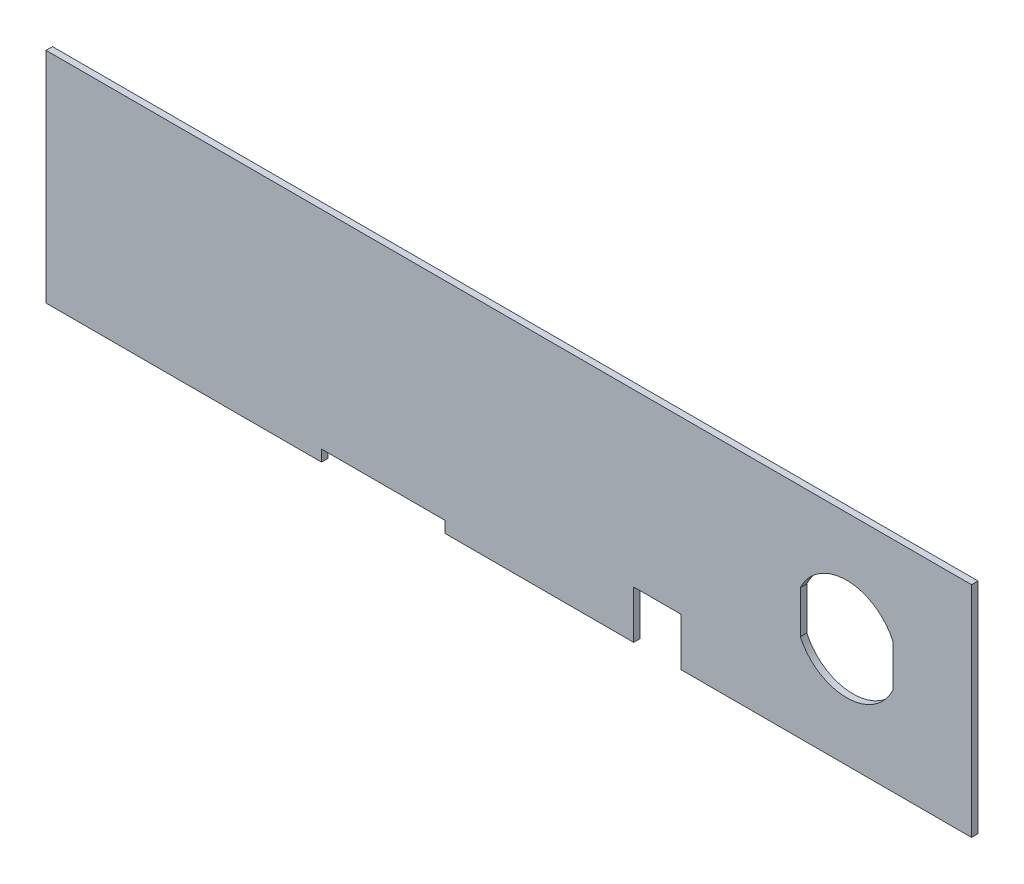
SolidWorks part; units mm, degrees
ref_plane "Front Plane" through (0, 0, 0) normal (0, 0, 1) x (1, 0, 0)
ref_plane "Top Plane" through (0, 0, 0) normal (0, 1, 0) x (1, 0, 0)
ref_plane "Right Plane" through (0, 0, 0) normal (1, 0, 0) x (0, 0, -1)
sketch "Sketch1" plane through (0, 0, 0) normal (0, 0, 1) x (1, 0, 0)
  line L0 (161.29, 0) -> (174.3202, 0)
  line L1 (0, 60.071) -> (254, 60.071)
  line L2 (0, 60.071) -> (0, 0)
  line L3 (0, 0) -> (254, 0)
  line L4 (254, 60.071) -> (254, 0)
  line L5 (92.5322, 0) -> (92.5322, 60.071) construction
  line L6 (75.6158, 3.1115) -> (109.4486, 3.1115)
  line L7 (75.6158, 3.1115) -> (75.6158, 0)
  line L8 (161.29, 0) -> (161.29, 13.1699)
  line L9 (161.29, 13.1699) -> (174.3202, 13.1699)
  line L10 (174.3202, 0) -> (174.3202, 13.1699)
  line L11 (75.6158, 0) -> (109.4486, 0)
  line L12 (109.4486, 3.1115) -> (109.4486, 0)
  line L13 (232.41, 24.2156) -> (232.41, 35.8554)
  line L14 (207.01, 24.2156) -> (207.01, 35.8554)
  circle A0 centre (219.71, 30.0355) radius 20.32 construction
  arc A1 (232.41, 35.8554) -> (207.01, 35.8554) centre (219.71, 30.0355) ccw
  arc A2 (207.01, 24.2156) -> (232.41, 24.2156) centre (219.71, 30.0355) ccw
  dimension "D3" = 40.64
  dimension "D6" = 27.94
  dimension "D1" = 254
  dimension "D2" = 60.071
  dimension "D4" = 13.1699
  dimension "D5" = 13.0302
  dimension "D7" = 219.71
  dimension "D8" = 161.29
  dimension "D9" = 30.0355
  dimension "D10" = 3.1115
  dimension "D11" = 33.8328
  dimension "D12" = 92.5322
  dimension "D13" = 25.4
extrude "Boss-Extrude2" add sketch "Sketch1" along normal blind 1.778 contours L6 L12 L3 L8 L9 L10 L4 L1 L2 L7 A2 L14 A1 L13
